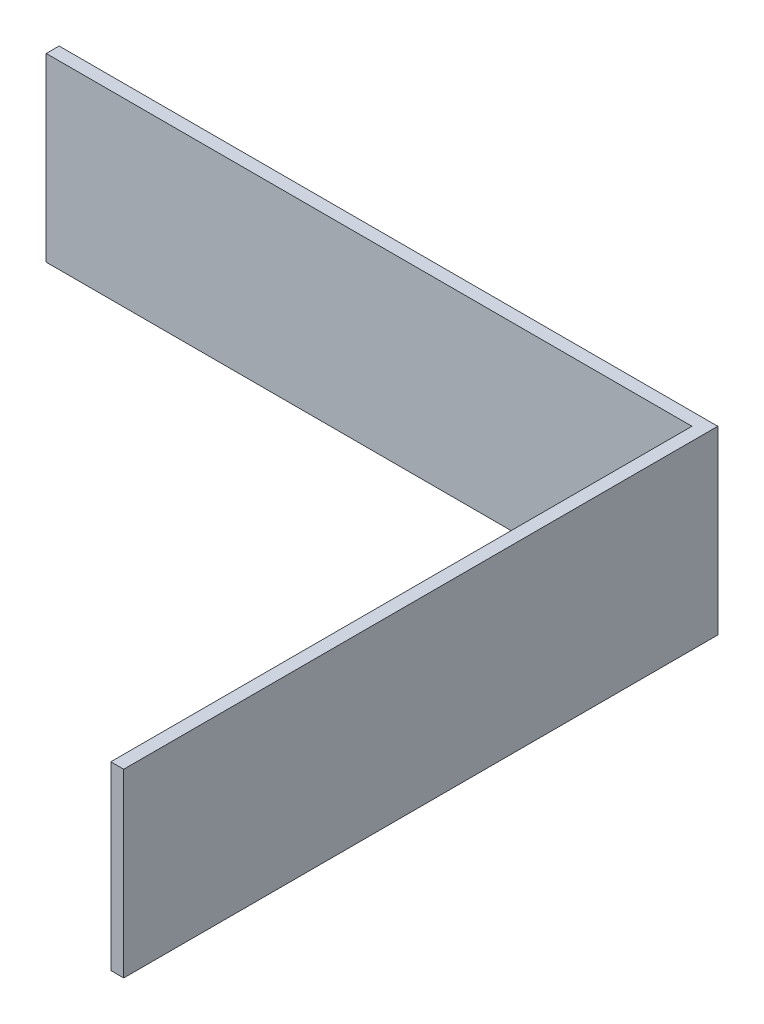
SolidWorks part; units mm, degrees
ref_plane "Front Plane" through (0, 0, 0) normal (0, 0, 1) x (1, 0, 0)
ref_plane "Top Plane" through (0, 0, 0) normal (0, 1, 0) x (1, 0, 0)
ref_plane "Right Plane" through (0, 0, 0) normal (1, 0, 0) x (0, 0, -1)
sketch "Sketch1" plane through (0, 0, 0) normal (0, 1, 0) x (1, 0, 0)
  line L0 (0, 0) -> (-500, 0)
  line L1 (-500, 0) -> (-500, 10)
  line L2 (-500, 10) -> (10, 10)
  line L3 (10, 10) -> (10, -450)
  line L4 (10, -450) -> (0, -450)
  line L5 (0, -450) -> (0, 0)
  dimension "D1" = 500
  dimension "D2" = 450
  dimension "D3" = 10
  dimension "D4" = 10
extrude "Boss-Extrude1" add sketch "Sketch1" along normal blind 140
